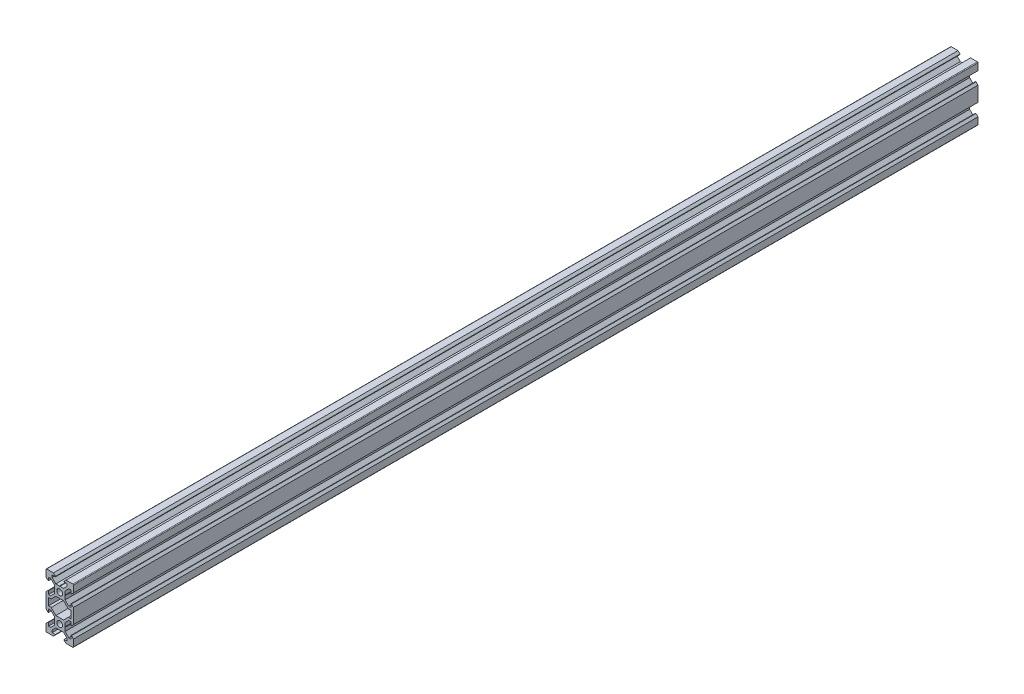
SolidWorks part; units mm, degrees
material "6061-T6 (SS)"
ref_plane "Front Plane" through (0, 0, 0) normal (0, 0, 1) x (1, 0, 0)
ref_plane "Top Plane" through (0, 0, 0) normal (0, 1, 0) x (1, 0, 0)
ref_plane "Right Plane" through (0, 0, 0) normal (1, 0, 0) x (0, 0, -1)
sketch "Sketch1" plane through (0, 0, 0) normal (0, 0, 1) x (1, 0, 0)
  line L0 (0, 0) -> (10, 0) construction
  line L1 (9.5, -20) -> (-9.5, -20)
  line L2 (10, -19.5) -> (10, 19.5)
  line L3 (9.5, 20) -> (-9.5, 20)
  line L4 (-10, -19.5) -> (-10, 19.5)
  line L5 (10, -20) -> (-10, 20) construction
  line L6 (10, 20) -> (-10, -20) construction
  circle A0 centre (0, 10) radius 2.1
  circle A1 centre (0, -10) radius 2.1
  arc A2 (-9.5, -20) -> (-10, -19.5) centre (-9.5, -19.5) cw
  arc A3 (9.5, -20) -> (10, -19.5) centre (9.5, -19.5) ccw
  arc A4 (10, 19.5) -> (9.5, 20) centre (9.5, 19.5) ccw
  arc A5 (-9.5, 20) -> (-10, 19.5) centre (-9.5, 19.5) ccw
  point P0 (0, 0)
  line B0 (0, 10) -> (0, 20) construction
  line B1 (0, 13.69) -> (-0.21, 13.9)
  line B2 (-0.21, 13.9) -> (-2.8393, 13.9)
  line B3 (-2.8393, 13.9) -> (-5.5, 16.5607)
  line B4 (-5.5, 16.5607) -> (-5.5, 18.2)
  line B5 (-5.5, 18.2) -> (-3.125, 18.2)
  line B6 (-3.125, 18.2) -> (-3.125, 18.545)
  line B7 (-3.125, 18.545) -> (-4.58, 20)
  line B8 (-4.58, 20) -> (4.58, 20)
  line B9 (0, 10) -> (-5.9132, 15.9132) construction
  line B10 (3.125, 18.545) -> (4.58, 20)
  line B11 (3.125, 18.2) -> (3.125, 18.545)
  line B12 (5.5, 18.2) -> (3.125, 18.2)
  line B13 (5.5, 16.5607) -> (5.5, 18.2)
  line B14 (2.8393, 13.9) -> (5.5, 16.5607)
  line B15 (0.21, 13.9) -> (2.8393, 13.9)
  line B16 (0, 13.69) -> (0.21, 13.9)
  line B17 (0, 10) -> (-10, 10) construction
  line B18 (-3.69, 10) -> (-3.9, 9.79)
  line B19 (-3.9, 9.79) -> (-3.9, 7.1607)
  line B20 (-3.9, 7.1607) -> (-6.5607, 4.5)
  line B21 (-6.5607, 4.5) -> (-8.2, 4.5)
  line B22 (-8.2, 4.5) -> (-8.2, 6.875)
  line B23 (-8.2, 6.875) -> (-8.545, 6.875)
  line B24 (-8.545, 6.875) -> (-10, 5.42)
  line B25 (-10, 5.42) -> (-10, 14.58)
  line B26 (0, 10) -> (-5.9132, 4.0868) construction
  line B27 (-8.545, 13.125) -> (-10, 14.58)
  line B28 (-8.2, 13.125) -> (-8.545, 13.125)
  line B29 (-8.2, 15.5) -> (-8.2, 13.125)
  line B30 (-6.5607, 15.5) -> (-8.2, 15.5)
  line B31 (-3.9, 12.8393) -> (-6.5607, 15.5)
  line B32 (-3.9, 10.21) -> (-3.9, 12.8393)
  line B33 (-3.69, 10) -> (-3.9, 10.21)
  line B34 (0, -10) -> (-10, -10) construction
  line B35 (-3.69, -10) -> (-3.9, -10.21)
  line B36 (-3.9, -10.21) -> (-3.9, -12.8393)
  line B37 (-3.9, -12.8393) -> (-6.5607, -15.5)
  line B38 (-6.5607, -15.5) -> (-8.2, -15.5)
  line B39 (-8.2, -15.5) -> (-8.2, -13.125)
  line B40 (-8.2, -13.125) -> (-8.545, -13.125)
  line B41 (-8.545, -13.125) -> (-10, -14.58)
  line B42 (-10, -14.58) -> (-10, -5.42)
  line B43 (0, -10) -> (-5.9132, -15.9132) construction
  line B44 (-8.545, -6.875) -> (-10, -5.42)
  line B45 (-8.2, -6.875) -> (-8.545, -6.875)
  line B46 (-8.2, -4.5) -> (-8.2, -6.875)
  line B47 (-6.5607, -4.5) -> (-8.2, -4.5)
  line B48 (-3.9, -7.1607) -> (-6.5607, -4.5)
  line B49 (-3.9, -9.79) -> (-3.9, -7.1607)
  line B50 (-3.69, -10) -> (-3.9, -9.79)
  line B51 (0, -10) -> (0, -20) construction
  line B52 (0, -13.69) -> (0.21, -13.9)
  line B53 (0.21, -13.9) -> (2.8393, -13.9)
  line B54 (2.8393, -13.9) -> (5.5, -16.5607)
  line B55 (5.5, -16.5607) -> (5.5, -18.2)
  line B56 (5.5, -18.2) -> (3.125, -18.2)
  line B57 (3.125, -18.2) -> (3.125, -18.545)
  line B58 (3.125, -18.545) -> (4.58, -20)
  line B59 (4.58, -20) -> (-4.58, -20)
  line B60 (0, -10) -> (5.9132, -15.9132) construction
  line B61 (-3.125, -18.545) -> (-4.58, -20)
  line B62 (-3.125, -18.2) -> (-3.125, -18.545)
  line B63 (-5.5, -18.2) -> (-3.125, -18.2)
  line B64 (-5.5, -16.5607) -> (-5.5, -18.2)
  line B65 (-2.8393, -13.9) -> (-5.5, -16.5607)
  line B66 (-0.21, -13.9) -> (-2.8393, -13.9)
  line B67 (0, -13.69) -> (-0.21, -13.9)
  line B68 (0, -10) -> (10, -10) construction
  line B69 (3.69, -10) -> (3.9, -9.79)
  line B70 (3.9, -9.79) -> (3.9, -7.1607)
  line B71 (3.9, -7.1607) -> (6.5607, -4.5)
  line B72 (6.5607, -4.5) -> (8.2, -4.5)
  line B73 (8.2, -4.5) -> (8.2, -6.875)
  line B74 (8.2, -6.875) -> (8.545, -6.875)
  line B75 (8.545, -6.875) -> (10, -5.42)
  line B76 (10, -5.42) -> (10, -14.58)
  line B77 (0, -10) -> (5.9132, -4.0868) construction
  line B78 (8.545, -13.125) -> (10, -14.58)
  line B79 (8.2, -13.125) -> (8.545, -13.125)
  line B80 (8.2, -15.5) -> (8.2, -13.125)
  line B81 (6.5607, -15.5) -> (8.2, -15.5)
  line B82 (3.9, -12.8393) -> (6.5607, -15.5)
  line B83 (3.9, -10.21) -> (3.9, -12.8393)
  line B84 (3.69, -10) -> (3.9, -10.21)
  line B85 (0, 10) -> (10, 10) construction
  line B86 (3.69, 10) -> (3.9, 10.21)
  line B87 (3.9, 10.21) -> (3.9, 12.8393)
  line B88 (3.9, 12.8393) -> (6.5607, 15.5)
  line B89 (6.5607, 15.5) -> (8.2, 15.5)
  line B90 (8.2, 15.5) -> (8.2, 13.125)
  line B91 (8.2, 13.125) -> (8.545, 13.125)
  line B92 (8.545, 13.125) -> (10, 14.58)
  line B93 (10, 14.58) -> (10, 5.42)
  line B94 (0, 10) -> (5.9132, 15.9132) construction
  line B95 (8.545, 6.875) -> (10, 5.42)
  line B96 (8.2, 6.875) -> (8.545, 6.875)
  line B97 (8.2, 4.5) -> (8.2, 6.875)
  line B98 (6.5607, 4.5) -> (8.2, 4.5)
  line B99 (3.9, 7.1607) -> (6.5607, 4.5)
  line B100 (3.9, 9.79) -> (3.9, 7.1607)
  line B101 (3.69, 10) -> (3.9, 9.79)
  line B102 (-8.2, -2.7) -> (-8.2, 2.7)
  line B103 (-8.2, 2.7) -> (-6.2393, 2.7)
  line B104 (-6.2393, 2.7) -> (-2.8393, 6.1)
  line B105 (-2.8393, 6.1) -> (2.8393, 6.1)
  line B106 (0, 6.1) -> (0, 0) construction
  line B107 (0, 0) -> (-8.2, 0) construction
  line B108 (6.2393, 2.7) -> (2.8393, 6.1)
  line B109 (8.2, 2.7) -> (6.2393, 2.7)
  line B110 (8.2, -2.7) -> (8.2, 2.7)
  line B111 (8.2, -2.7) -> (6.2393, -2.7)
  line B112 (6.2393, -2.7) -> (2.8393, -6.1)
  line B113 (-2.8393, -6.1) -> (2.8393, -6.1)
  line B114 (-6.2393, -2.7) -> (-2.8393, -6.1)
  line B115 (-8.2, -2.7) -> (-6.2393, -2.7)
  line B116 (0, 6.1) -> (0, 10) construction
  line B117 (0, 10) -> (-5.0927, 4.9073) construction
sketch_block_instance "V Slot 1-4"
sketch_block "V Slot 1" parameters "D1"=10, "D2"=11, "D3"=4.3, "D4"=1.8, "D5"=0.21, "D6"=45, "D7"=9.16, "D8"=1.5, "D9"=6.25
sketch_block_instance "V Slot 1-5"
sketch_block_instance "V Slot 1-6"
sketch_block_instance "V Slot 1-7"
sketch_block_instance "V Slot 1-8"
sketch_block_instance "V Slot 1-9"
sketch_block_instance "Center Cutout 1-1"
sketch_block "Center Cutout 1" parameters "D1"=5.4, "D2"=12.2, "D3"=8.2, "D4"=45, "D5"=10, "D6"=1.5
extrude "Boss-Extrude1" add sketch "Sketch1" along normal blind 660 contours B101 B86 B87 B88 B89 B90 B91 B92 L2 A4 L3 B10 B11 B12 B13 B14 B15 B16 B1 B2 B3 B4 B5 B6 B7 A5 L4 B27 B28 B29 B30 B31 B32 B33 B18 B19 B20 B21 B22 B23 B24 B44 B45 B46 B47 B48 B49 B50 B35
